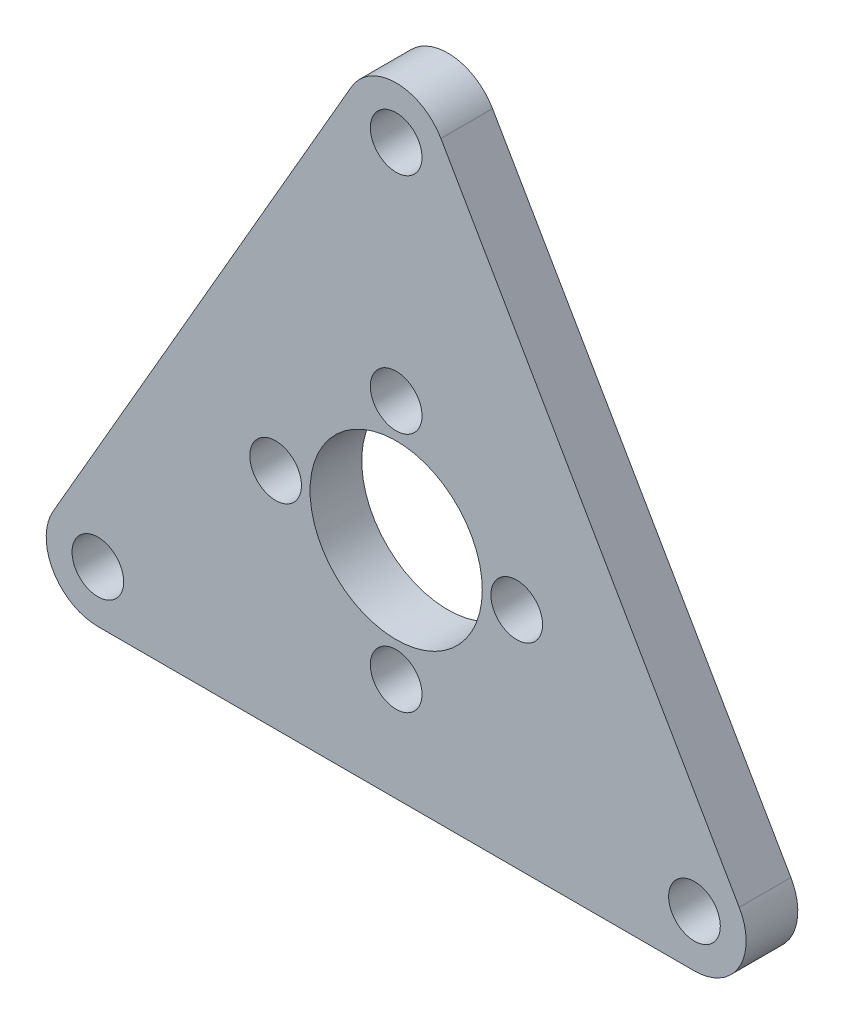
SolidWorks part; units mm, degrees
material "Thornel Mat VMA"
ref_plane "前视基准面" through (0, 0, 0) normal (0, 0, 1) x (1, 0, 0)
ref_plane "上视基准面" through (0, 0, 0) normal (0, 1, 0) x (1, 0, 0)
ref_plane "右视基准面" through (0, 0, 0) normal (1, 0, 0) x (0, 0, -1)
sketch "草图1" plane through (0, 0, 0) normal (0, 0, 1) x (1, 0, 0)
  line L0 (0, 20) -> (-17.3205, -10) construction
  line L1 (-17.3205, -10) -> (17.3205, -10) construction
  line L2 (17.3205, -10) -> (0, 20) construction
  line L3 (-2.5981, 21.5) -> (-19.9186, -8.5)
  line L4 (-17.3205, -13) -> (17.3205, -13)
  line L5 (19.9186, -8.5) -> (2.5981, 21.5)
  circle A0 centre (0, 0) radius 20 construction
  circle A1 centre (-17.3205, -10) radius 1.5
  circle A2 centre (0, 20) radius 1.5
  circle A3 centre (17.3205, -10) radius 1.5
  circle A4 centre (0, 0) radius 5
  circle A5 centre (0, 0) radius 7 construction
  circle A6 centre (0, 7) radius 1.5
  circle A7 centre (0, -7) radius 1.5
  circle A8 centre (0, 0) radius 26 construction
  arc A9 (-19.9186, -8.5) -> (-17.3205, -13) centre (-17.3205, -10) ccw
  arc A10 (17.3205, -13) -> (19.9186, -8.5) centre (17.3205, -10) ccw
  arc A11 (-2.5981, 21.5) -> (2.5981, 21.5) centre (0, 20) cw
  circle A12 centre (-7, 0) radius 1.5
  circle A13 centre (7, 0) radius 1.5
  point P23 (-22.5167, -13)
  point P26 (22.5167, -13)
  point P29 (0, 26)
  dimension "D1" = 40
  dimension "D2" = 3
  dimension "D3" = 10
  dimension "D4" = 14
  dimension "D5" = 3
  dimension "D6" = 3
  dimension "D7" = 3
extrude "凸台-拉伸1" add sketch "草图1" along normal blind 3
